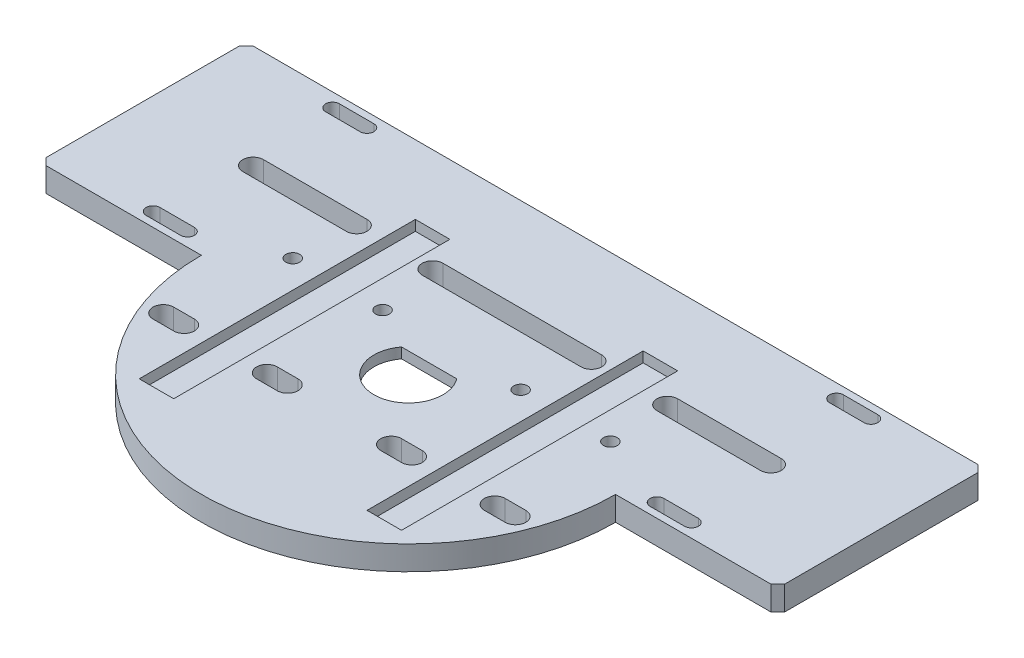
SolidWorks part; units mm, degrees
material "Alloy Steel (SS)"
ref_plane "Front Plane" through (0, 0, 0) normal (0, 0, 1) x (1, 0, 0)
ref_plane "Top Plane" through (0, 0, 0) normal (0, 1, 0) x (1, 0, 0)
ref_plane "Right Plane" through (0, 0, 0) normal (1, 0, 0) x (0, 0, -1)
sketch "Sketch1" plane through (0, 0, 0) normal (0, 1, 0) x (1, 0, 0)
  line L0 (-28, 0) -> (28, 0) construction
  circle A0 centre (0, 0) radius 60
  point P7 (0, 0)
  dimension "D1" = 120
  dimension "D2" = 56
extrude "Boss-Extrude1" add sketch "Sketch1" against normal blind 7 contours A0
sketch "Sketch2" plane through (0, 0, 0) normal (0, 1, 0) x (1, 0, 0)
  line L0 (0, 0) -> (0, 19.372) construction
  line L1 (-38, 40) -> (-28, 40)
  line L2 (-38, 40) -> (-38, -40)
  line L3 (-38, -40) -> (-28, -40)
  line L4 (-28, 40) -> (-28, -40)
  line L5 (-38, 40) -> (-28, -40) construction
  line L6 (-38, -40) -> (-28, 40) construction
  line L7 (38, -40) -> (28, -40)
  line L8 (38, 40) -> (28, 40)
  line L9 (38, 40) -> (38, -40)
  line L10 (28, 40) -> (28, -40)
  point P0 (-33, 0)
  point P5 (-28, 0)
  dimension "D1" = 10
  dimension "D2" = 80
extrude "Boss-Extrude2" add sketch "Sketch2" along normal blind 163
sketch "Sketch8" plane through (0, 0, 0) normal (0, 1, 0) x (1, 0, 0)
  line L1 (-90, 5) -> (90, 5)
  line L2 (-90, 5) -> (-90, 55)
  line L3 (-90, 55) -> (90, 55)
  line L4 (90, 5) -> (90, 55)
  line L5 (-90, 5) -> (90, 55) construction
  line L6 (-90, 55) -> (90, 5) construction
  point P0 (0, 30)
  dimension "D1" = 30
  dimension "D2" = 50
  dimension "D3" = 180
  dimension "D4" = 5
extrude "Boss-Extrude5" add sketch "Sketch8" against normal up to surface (7 mm away) up to face at (0, -7, 60)
chamfer "Chamfer1" distance 2 angle 45 4 edges at (-90, -3.5, -5) (-90, -3.5, -55) (90, -3.5, -55) (90, -3.5, -5)
sketch "Sketch9" plane through (0, 0, 0) normal (0, 1, 0) x (1, 0, 0)
  line L0 (90, 30) -> (-90, 30) construction
  line L1 (90, 7) -> (90, 53) construction
  line L2 (-90, 53) -> (-90, 7) construction
  line L3 (45, 30) -> (75, 30) construction
  line L4 (45, 33) -> (75, 33)
  line L5 (45, 27) -> (75, 27)
  line L6 (38, -40) -> (38, 40) construction
  line L7 (88, 55) -> (23.9792, 55) construction
  arc A0 (45, 33) -> (45, 27) centre (45, 30) ccw
  arc A1 (75, 27) -> (75, 33) centre (75, 30) ccw
  point P8 (60, 30)
  dimension "D3" = 3
  dimension "D1" = 30
  dimension "D2" = 7
  dimension "D4" = 25
extrude "Cut-Extrude3" cut sketch "Sketch9" against normal up to surface (7 mm away) up to face at (0, -7, -25)
mirror "Mirror4" about plane through (0, 0, 0) normal (1, 0, 0) of "Cut-Extrude3"
sketch "Sketch10" plane through (0, 0, 0) normal (0, 1, 0) x (1, 0, 0)
  circle A0 centre (0, 0) radius 10
  dimension "D1" = 20
extrude "Cut-Extrude4" cut sketch "Sketch10" against normal up to next
sketch "Sketch12" plane through (0, 0, 0) normal (0, 0, 1) x (1, 0, 0)
  line L0 (0, -7) -> (0, -3.5)
  line L4 (-10, -7) -> (10, -7) construction
  line L6 (0, -3.5) -> (-14.5, -3.5)
  line L7 (-21.5, -3.5) -> (-21.5, -7)
  line L8 (-23.9792, -7) -> (23.9792, -7) construction
  line L9 (-21.5, -7) -> (0, -7)
  line L10 (-14.5, -3.5) -> (-14.5, -3)
  line L11 (-14.5, -3) -> (-21.5, -3)
  line L12 (-21.5, -3) -> (-21.5, -3.5)
  dimension "D1" = 3.5
  dimension "D2" = 21.5
  dimension "D3" = 0.5
  dimension "D4" = 7
  dimension "D5" = 21.5
revolve "Cut-Revolve1" cut sketch "Sketch12" angle 360 about L0
sketch "Sketch13" plane through (0, -3.5, 0) normal (0, -1, 0) x (1, 0, 0)
  line L0 (0, 0) -> (0, 10) construction
  line L1 (-8, -6) -> (8, -6)
  circle A0 centre (0, 0) radius 10 construction
  circle A1 centre (0, 0) radius 10
  dimension "D1" = 6
sketch "Sketch14" plane through (0, 0, 0) normal (0, 1, 0) x (1, 0, 0)
  line L0 (-8, 6) -> (8, 6) construction
  line L1 (-8, 6) -> (8, 6)
  circle A2 centre (0, 0) radius 10
  circle A3 centre (0, 0) radius 10
  circle M2 centre (0, 0) radius 10
  dimension "D1" = 0
extrude "Boss-Extrude6" add sketch "Sketch14" against normal up to surface (3 mm away) contours L1 M2
sketch "Sketch15" plane through (0, 163, 0) normal (0, 1, 0) x (1, 0, 0)
  line L0 (38, 40) -> (28, 40) construction
  line L1 (28, 40) -> (28, -40) construction
  line L2 (38, -40) -> (38, 40) construction
  line L3 (28, -40) -> (38, -40) construction
  line L4 (-38, -40) -> (-28, -40) construction
  line L5 (-28, -40) -> (-28, 40) construction
  line L6 (-28, 40) -> (-38, 40) construction
  line L7 (-38, 40) -> (-38, -40) construction
  line L8 (38, 40) -> (28, 40)
  line L9 (28, 40) -> (28, -40)
  line L10 (38, -40) -> (38, 40)
  line L11 (28, -40) -> (38, -40)
  line L12 (-38, -40) -> (-28, -40)
  line L13 (-28, -40) -> (-28, 40)
  line L14 (-28, 40) -> (-38, 40)
  line L15 (-38, 40) -> (-38, -40)
extrude "Cut-Extrude5" cut sketch "Sketch15" against normal blind 166
sketch "Sketch16" plane through (0, 0, 0) normal (0, 1, 0) x (1, 0, 0)
  line L0 (-51, -20) -> (-45, -20) construction
  line L1 (-51, -17) -> (-45, -17)
  line L2 (-51, -23) -> (-45, -23)
  line L3 (-45, 27) -> (-75, 27) construction
  line L4 (0, 0) -> (0, -22.8846) construction
  line L5 (51, -20) -> (45, -20) construction
  line L6 (51, -17) -> (45, -17)
  line L7 (51, -23) -> (45, -23)
  line L8 (-78, 30) -> (-42, 30) construction
  arc A0 (-51, -17) -> (-51, -23) centre (-51, -20) ccw
  arc A1 (-45, -23) -> (-45, -17) centre (-45, -20) ccw
  arc A2 (-45, 27) -> (-45, 33) centre (-45, 30) ccw construction
  arc A3 (51, -17) -> (51, -23) centre (51, -20) cw
  arc A4 (45, -23) -> (45, -17) centre (45, -20) cw
  arc A5 (-75, 33) -> (-75, 27) centre (-75, 30) ccw construction
  point P2 (-48, -20)
  point P9 (-60, 27)
  point P14 (-42, 30)
  point P15 (-42, -20)
  point P20 (48, -20)
  dimension "D1" = 47
  dimension "D2" = 6
  dimension "D3" = 50
extrude "Cut-Extrude6" cut sketch "Sketch16" against normal up to next
sketch "Sketch17" plane through (0, 0, 0) normal (0, 1, 0) x (1, 0, 0)
  line L0 (-23, 30) -> (23, 30) construction
  line L1 (-23, 33) -> (23, 33)
  line L2 (-23, 27) -> (23, 27)
  line L3 (-33, 40) -> (-33, -40) construction
  line L6 (-28, 40) -> (-38, 40) construction
  line L7 (-38, -40) -> (-28, -40) construction
  line L8 (33, 40) -> (33, -40) construction
  line L9 (38, 40) -> (28, 40) construction
  line L10 (28, -40) -> (38, -40) construction
  line L11 (45, -23) -> (51, -23) construction
  line L12 (51, -17) -> (45, -17) construction
  line L13 (-45, -17) -> (-51, -17) construction
  line L14 (-51, -23) -> (-45, -23) construction
  line L15 (45, -23) -> (51, -23)
  line L16 (51, -17) -> (45, -17)
  line L17 (-45, -17) -> (-51, -17)
  line L18 (-51, -23) -> (-45, -23)
  line L19 (-15, -23) -> (-21, -23)
  line L20 (-21, -17) -> (-15, -17)
  line L21 (15, -17) -> (21, -17)
  line L22 (21, -23) -> (15, -23)
  arc A0 (-23, 33) -> (-23, 27) centre (-23, 30) ccw
  arc A1 (23, 27) -> (23, 33) centre (23, 30) ccw
  arc A4 (-45, 27) -> (-45, 33) centre (-45, 30) ccw construction
  arc A7 (51, -23) -> (51, -17) centre (51, -20) ccw construction
  arc A8 (45, -17) -> (45, -23) centre (45, -20) ccw construction
  arc A9 (-51, -17) -> (-51, -23) centre (-51, -20) ccw construction
  arc A10 (-45, -23) -> (-45, -17) centre (-45, -20) ccw construction
  arc A11 (51, -23) -> (51, -17) centre (51, -20) ccw
  arc A12 (45, -17) -> (45, -23) centre (45, -20) ccw
  arc A13 (-51, -17) -> (-51, -23) centre (-51, -20) ccw
  arc A14 (-45, -23) -> (-45, -17) centre (-45, -20) ccw
  arc A15 (-21, -23) -> (-21, -17) centre (-21, -20) cw
  arc A16 (-15, -17) -> (-15, -23) centre (-15, -20) cw
  arc A17 (21, -17) -> (21, -23) centre (21, -20) cw
  arc A18 (15, -23) -> (15, -17) centre (15, -20) cw
  point P3 (0, 30)
  point P19 (-42, 30)
  dimension "D2" = 22
  dimension "D1" = 46
extrude "Cut-Extrude8" cut sketch "Sketch17" against normal up to next contours A15 L20 A16 L19 | A17 L22 A18 L21 | L2 A1 L1 A0
sketch "Sketch18" plane through (0, 0, 0) normal (0, 1, 0) x (1, 0, 0)
  line L0 (-90, 53) -> (-90, 7) construction
  line L1 (-23.9792, 55) -> (-88, 55) construction
  circle A0 centre (-46, 12.5) radius 2
  circle A1 centre (-20, 12.5) radius 2
  circle A2 centre (20, 12.5) radius 2
  circle A3 centre (46, 12.5) radius 2
  dimension "D1" = 44
  dimension "D3" = 4
  dimension "D2" = 42.5
extrude "Cut-Extrude9" cut sketch "Sketch18" against normal up to next
sketch "Sketch19" plane through (0, 0, 0) normal (0, 1, 0) x (1, 0, 0)
  line L0 (-90, 50) -> (-90, 60)
  line L1 (-90, 53) -> (-90, 7) construction
  line L2 (-90, 60) -> (90, 60)
  line L3 (90, 60) -> (90, 50)
  line L5 (-90, 50) -> (90, 50)
  line L6 (90, 7) -> (90, 53) construction
  line L7 (90, 7) -> (58, 7)
  line L10 (58, 0) -> (90, 0)
  line L12 (58, 7) -> (58, 0)
  line L13 (90, 7) -> (90, 0)
  line L14 (0, 0) -> (0, 15.8804) construction
  line L15 (59.7913, 5) -> (88, 5) construction
  line L16 (88, 55) -> (23.9792, 55) construction
  line L17 (-90, 7) -> (-90, 0)
  line L18 (-58, 7) -> (-58, 0)
  line L19 (-58, 0) -> (-90, 0)
  line L20 (-90, 7) -> (-58, 7)
  dimension "D1" = 50
  dimension "D2" = 5
  dimension "D3" = 5
  dimension "D4" = 58
extrude "Boss-Extrude7" add sketch "Sketch19" against normal up to surface (7 mm away) up to face at (-46, -7, -10.5)
sketch "Sketch20" plane through (0, 0, 0) normal (0, 1, 0) x (1, 0, 0)
  line L0 (-78, 4) -> (-68, 4) construction
  line L1 (-78, 6) -> (-68, 6)
  line L2 (-78, 2) -> (-68, 2)
  line L3 (-90, 60) -> (-90, 0) construction
  line L4 (-90, 0) -> (-60, 0) construction
  line L5 (-90, 30) -> (-76.6508, 30) construction
  line L6 (-78, 56) -> (-68, 56) construction
  line L7 (-78, 54) -> (-68, 54)
  line L8 (-78, 58) -> (-68, 58)
  line L9 (0, 0) -> (0, 31.2915) construction
  line L10 (-78, 56) -> (-68, 56) construction
  line L11 (-78, 54) -> (-68, 54)
  line L12 (-78, 58) -> (-68, 58)
  line L13 (-78, 4) -> (-68, 4) construction
  line L14 (-78, 6) -> (-68, 6)
  line L15 (-78, 2) -> (-68, 2)
  line L16 (78, 56) -> (68, 56) construction
  line L17 (78, 54) -> (68, 54)
  line L18 (78, 58) -> (68, 58)
  line L19 (78, 56) -> (68, 56) construction
  line L20 (78, 54) -> (68, 54)
  line L21 (78, 58) -> (68, 58)
  line L22 (78, 4) -> (68, 4) construction
  line L23 (78, 6) -> (68, 6)
  line L24 (78, 2) -> (68, 2)
  line L25 (78, 4) -> (68, 4) construction
  line L26 (78, 6) -> (68, 6)
  line L27 (78, 2) -> (68, 2)
  arc A0 (-78, 6) -> (-78, 2) centre (-78, 4) ccw
  arc A1 (-68, 2) -> (-68, 6) centre (-68, 4) ccw
  arc A2 (-78, 54) -> (-78, 58) centre (-78, 56) cw
  arc A3 (-68, 58) -> (-68, 54) centre (-68, 56) cw
  arc A4 (-78, 54) -> (-78, 58) centre (-78, 56) cw
  arc A5 (-68, 58) -> (-68, 54) centre (-68, 56) cw
  arc A6 (-78, 6) -> (-78, 2) centre (-78, 4) ccw
  arc A7 (-68, 2) -> (-68, 6) centre (-68, 4) ccw
  arc A8 (78, 54) -> (78, 58) centre (78, 56) ccw
  arc A9 (68, 58) -> (68, 54) centre (68, 56) ccw
  arc A10 (78, 54) -> (78, 58) centre (78, 56) ccw
  arc A11 (68, 58) -> (68, 54) centre (68, 56) ccw
  arc A12 (78, 6) -> (78, 2) centre (78, 4) cw
  arc A13 (68, 2) -> (68, 6) centre (68, 4) cw
  arc A14 (78, 6) -> (78, 2) centre (78, 4) cw
  arc A15 (68, 2) -> (68, 6) centre (68, 4) cw
  point P2 (-73, 4)
  point P11 (-73, 2)
  point P16 (-73, 56)
  point P26 (-73, 56)
  point P33 (-73, 4)
  point P40 (73, 56)
  point P47 (73, 56)
  point P54 (73, 4)
  point P61 (73, 4)
  dimension "D1" = 12
  dimension "D2" = 10
  dimension "D3" = 4
  dimension "D4" = 4
extrude "Cut-Extrude10" cut sketch "Sketch20" against normal blind 10 contours A13 L24 A12 L23 | L18 A9 L17 A8 | A3 L8 A2 L7 | L2 A1 L1 A0
chamfer "Chamfer2" distance 3 angle 45 4 edges at (-90, -3.5, 0) (-90, -3.5, -60) (90, -3.5, 0) (90, -3.5, -60)
sketch "Sketch21" plane through (0, 0, 0) normal (1, 0, 0) x (0, 0, -1)
  line L0 (0, 0) -> (0, -3.5) construction
  line L1 (-10, -3.5) -> (10, -3.5) construction
  line L2 (0, -3.5) -> (15, -3.5)
  line L3 (15, -3.5) -> (15, -3)
  line L5 (15, -3) -> (0, -3)
  line L7 (0, -3.5) -> (0, -3)
  dimension "D1" = 0.5
  dimension "D2" = 15
revolve "Cut-Revolve2" cut sketch "Sketch21" angle 360 about L0
sketch "Sketch22" plane through (0, -3, 0) normal (0, -1, 0) x (1, 0, 0)
  circle A0 centre (0, 0) radius 15
  circle A1 centre (0, 0) radius 16
  dimension "D2" = 30
  dimension "D1" = 1
extrude "Boss-Extrude8" add sketch "Sketch22" along normal blind 1.5
sketch "Sketch23" plane through (0, 0, 0) normal (0, 1, 0) x (1, 0, 0)
  line L0 (0, 0) -> (0, 27) construction
  line L1 (-87, 60) -> (-107, 60)
  line L2 (-87, 60) -> (-87, 0)
  line L3 (-87, 0) -> (-107, 0)
  line L4 (-107, 60) -> (-107, 0)
  line L5 (-23, 27) -> (23, 27) construction
  line L6 (87, 0) -> (107, 0)
  line L7 (107, 60) -> (107, 0)
  line L8 (87, 60) -> (107, 60)
  line L9 (87, 60) -> (87, 0)
  dimension "D1" = 20
  dimension "D2" = 60
extrude "Boss-Extrude9" add sketch "Sketch23" against normal up to surface (7 mm away) up to face at (-73, -7, -4)
chamfer "Chamfer3" distance 2 angle 45 4 edges at (107, -3.5, -60) (107, -3.5, 0) (-107, -3.5, -60) (-107, -3.5, 0)
